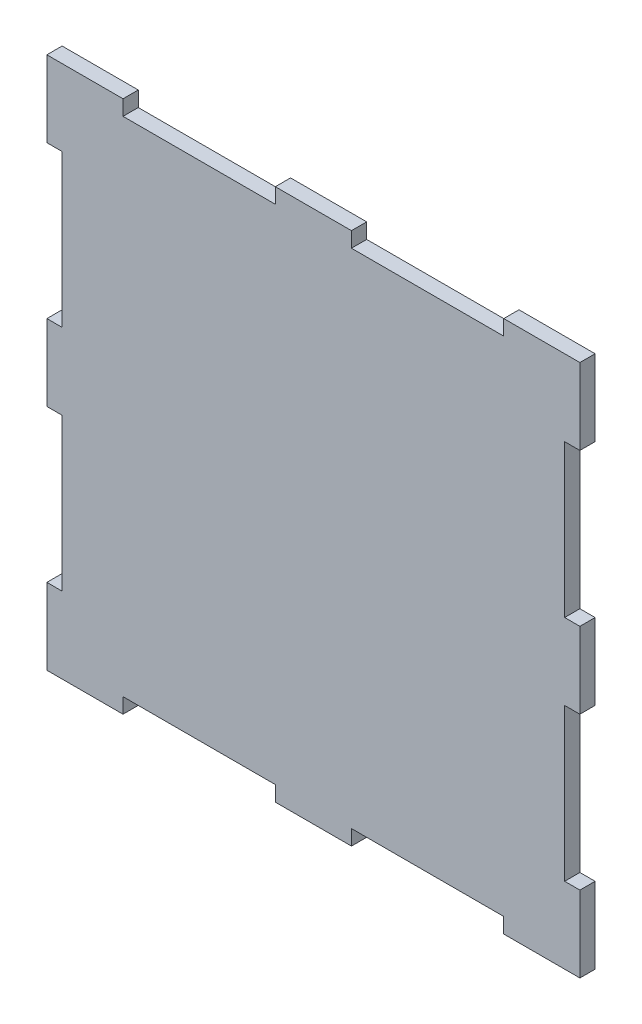
SolidWorks part; units mm, degrees
ref_plane "Front Plane" through (0, 0, 0) normal (0, 0, 1) x (1, 0, 0)
ref_plane "Top Plane" through (0, 0, 0) normal (0, 1, 0) x (1, 0, 0)
ref_plane "Right Plane" through (0, 0, 0) normal (1, 0, 0) x (0, 0, -1)
sketch "Sketch1" plane through (0, 0, 0) normal (0, 0, 1) x (1, 0, 0)
  line L1 (-35, -35) -> (35, -35)
  line L2 (-35, -35) -> (-35, 35)
  line L3 (-35, 35) -> (35, 35)
  line L4 (35, -35) -> (35, 35)
  line L5 (0, 35) -> (0, -35) construction
  line L6 (-35, 0) -> (35, 0) construction
  dimension "D1" = 70
  dimension "D2" = 70
extrude "Boss-Extrude1" add sketch "Sketch1" against normal blind 2
sketch "Sketch2" plane through (0, 0, 0) normal (0, 0, 1) x (1, 0, 0)
  line L0 (-35, 35) -> (-25, 35)
  line L1 (35, 35) -> (-35, 35) construction
  line L2 (-25, 35) -> (-5, 35)
  line L3 (-5, 35) -> (5, 35)
  line L4 (5, 35) -> (25, 35)
  line L6 (35, 35) -> (35, 25)
  line L7 (-25, 33) -> (-5, 33)
  line L8 (-25, 33) -> (-25, 37)
  line L9 (-25, 37) -> (-5, 37)
  line L10 (-5, 33) -> (-5, 37)
  line L11 (-15, 37) -> (-15, 33) construction
  line L12 (-25, 35) -> (-5, 35) construction
  line L13 (5, 33) -> (25, 33)
  line L14 (5, 33) -> (5, 37)
  line L15 (5, 37) -> (25, 37)
  line L16 (25, 33) -> (25, 37)
  line L17 (15, 37) -> (15, 33) construction
  line L18 (5, 35) -> (25, 35) construction
  line L19 (35, -35) -> (35, 35) construction
  line L20 (35, 25) -> (35, 5)
  line L21 (35, 5) -> (35, -5)
  line L22 (35, -5) -> (35, -25)
  line L23 (-35, -35) -> (-25, -35)
  line L24 (35, -5) -> (33, -5)
  line L25 (35, -5) -> (35, -25)
  line L26 (35, -25) -> (33, -25)
  line L27 (33, -5) -> (33, -25)
  line L28 (35, 25) -> (33, 25)
  line L29 (35, 25) -> (35, 5)
  line L30 (35, 5) -> (33, 5)
  line L31 (33, 25) -> (33, 5)
  line L32 (-35, -35) -> (35, -35) construction
  line L33 (-25, -35) -> (-5, -35)
  line L34 (-5, -35) -> (5, -35)
  line L35 (5, -35) -> (25, -35)
  line L36 (-35, 35) -> (-35, 25)
  line L37 (-25, -35) -> (-5, -35)
  line L38 (-25, -35) -> (-25, -33)
  line L39 (-25, -33) -> (-5, -33)
  line L40 (-5, -35) -> (-5, -33)
  line L41 (5, -35) -> (25, -35)
  line L42 (5, -35) -> (5, -33)
  line L43 (5, -33) -> (25, -33)
  line L44 (25, -35) -> (25, -33)
  line L45 (-35, 35) -> (-35, -35) construction
  line L46 (-35, 25) -> (-35, 5)
  line L47 (-35, 5) -> (-35, -5)
  line L48 (-35, -5) -> (-35, -25)
  line L50 (-35, 25) -> (-33, 25)
  line L51 (-35, 25) -> (-35, 5)
  line L52 (-35, 5) -> (-33, 5)
  line L53 (-33, 25) -> (-33, 5)
  line L54 (-35, -5) -> (-33, -5)
  line L55 (-35, -5) -> (-35, -25)
  line L56 (-35, -25) -> (-33, -25)
  line L57 (-33, -5) -> (-33, -25)
  point P7 (15, 35)
  point P9 (-15, 35)
  point P10 (-15, 35)
  point P14 (15, 35)
  line M25 (35, -35) -> (35, 35)
  line M26 (35, 35) -> (-35, 35)
  line M27 (-35, 35) -> (-35, -35)
  line M28 (-35, -35) -> (35, -35)
  dimension "D1" = 10
  dimension "D2" = 20
  dimension "D3" = 10
  dimension "D4" = 20
  dimension "D5" = 4
  dimension "D6" = 20
  dimension "D7" = 20
  dimension "D8" = 4
  dimension "D9" = 10
  dimension "D10" = 20
  dimension "D11" = 10
  dimension "D12" = 20
  dimension "D13" = 2
  dimension "D14" = 2
  dimension "D15" = 10
  dimension "D16" = 20
  dimension "D17" = 10
  dimension "D18" = 20
  dimension "D19" = 20
  dimension "D20" = 20
  dimension "D21" = 2
  dimension "D22" = 2
  dimension "D23" = 10
  dimension "D24" = 20
  dimension "D25" = 10
  dimension "D26" = 20
  dimension "D27" = 2
  dimension "D28" = 2
extrude "Cut-Extrude1" cut sketch "Sketch2" against normal blind 2 contours L53 L50 L52 M27 | L57 L54 L56 M27 | L40 L39 L38 M28 | L44 L43 L42 M28 | L24 L27 L26 M25 | L28 L31 L30 M25 | L13 L16 L14 M26 | L7 L10 L8 M26
